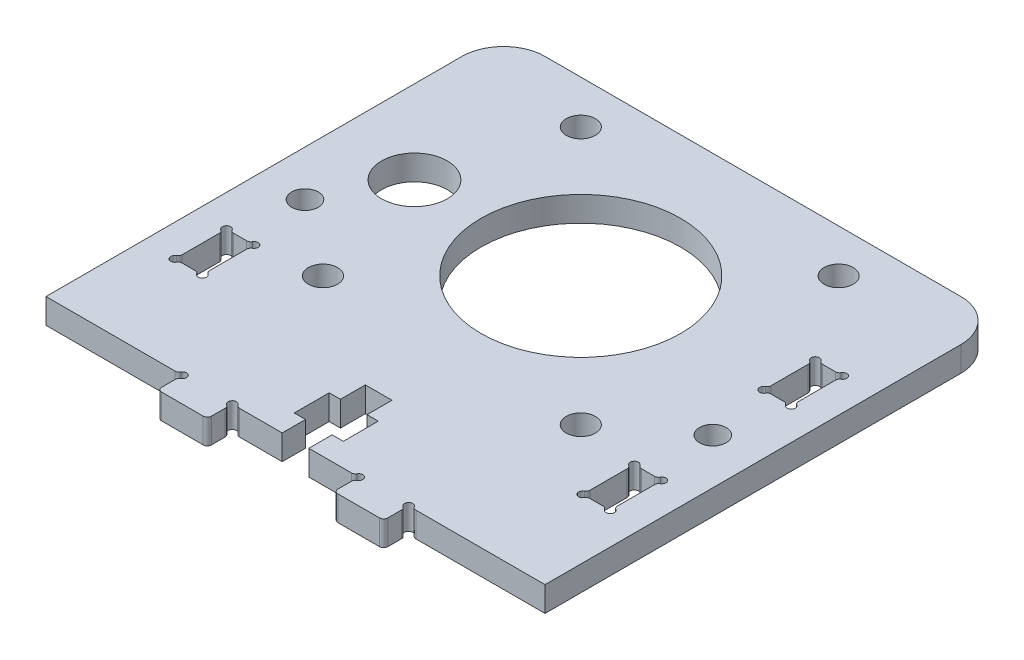
SolidWorks part; units mm, degrees
material "Plain Carbon Steel"
ref_plane "Front Plane" through (0, 0, 0) normal (0, 0, 1) x (1, 0, 0)
ref_plane "Top Plane" through (0, 0, 0) normal (0, 1, 0) x (1, 0, 0)
ref_plane "Right Plane" through (0, 0, 0) normal (1, 0, 0) x (0, 0, -1)
sketch "Sketch1" plane through (0, 0, 0) normal (0, 1, 0) x (1, 0, 0)
  line L0 (365.2434, 1060.953) -> (365.2434, 1056.485)
  line L1 (367.6773, 1061.819) -> (366.1094, 1061.819)
  line L3 (312.3734, 1022.1903) -> (327.9073, 1022.1903)
  line L4 (312.3734, 1072.1903) -> (312.3734, 1022.1903)
  line L5 (316.2034, 1039.1936) -> (316.2034, 1034.7256)
  line L6 (318.6373, 1040.0596) -> (317.0694, 1040.0596)
  line L7 (368.5433, 1034.7256) -> (368.5433, 1039.1936)
  line L8 (366.1094, 1033.8596) -> (367.6773, 1033.8596)
  line L9 (365.2434, 1039.1936) -> (365.2434, 1034.7256)
  line L10 (367.6773, 1040.0596) -> (366.1094, 1040.0596)
  line L14 (319.5033, 1034.7256) -> (319.5033, 1039.1936)
  line L15 (317.0694, 1033.8596) -> (318.6373, 1033.8596)
  line L16 (366.1094, 1055.619) -> (367.6773, 1055.619)
  line L17 (343.9733, 1022.1903) -> (349.1073, 1022.1903)
  line L18 (343.9733, 1024.9903) -> (343.9733, 1022.1903)
  line L19 (345.3233, 1024.9903) -> (343.9733, 1024.9903)
  line L20 (345.3233, 1029.1903) -> (345.3233, 1024.9903)
  line L21 (343.9733, 1029.1903) -> (345.3233, 1029.1903)
  line L22 (343.9733, 1032.1903) -> (343.9733, 1029.1903)
  line L23 (367.3733, 1077.1903) -> (317.3733, 1077.1903)
  line L24 (372.3733, 1022.1903) -> (372.3733, 1072.1903)
  line L25 (356.8394, 1022.1903) -> (372.3733, 1022.1903)
  line L26 (355.9733, 1019.6902) -> (355.9733, 1021.3243)
  line L27 (350.4733, 1019.1902) -> (355.4733, 1019.1902)
  line L28 (349.9733, 1021.3243) -> (349.9733, 1019.6902)
  line L29 (340.7733, 1032.1903) -> (343.9733, 1032.1903)
  line L30 (340.7733, 1029.1903) -> (340.7733, 1032.1903)
  line L31 (339.4233, 1029.1903) -> (340.7733, 1029.1903)
  line L32 (339.4233, 1024.9903) -> (339.4233, 1029.1903)
  line L33 (340.7733, 1024.9903) -> (339.4233, 1024.9903)
  line L34 (340.7733, 1022.1903) -> (340.7733, 1024.9903)
  line L35 (335.6394, 1022.1903) -> (340.7733, 1022.1903)
  line L36 (368.5433, 1056.485) -> (368.5433, 1060.953)
  line L37 (334.7733, 1019.6902) -> (334.7733, 1021.3243)
  line L38 (329.2733, 1019.1902) -> (334.2733, 1019.1902)
  line L39 (328.7733, 1021.3243) -> (328.7733, 1019.6902)
  line L40 (372.3733, 1022.1903) -> (312.3734, 1022.1903) construction
  line L41 (317.8533, 1047.1903) -> (317.8533, 1081.5508) construction
  line L42 (368.0078, 1047.1903) -> (368.0078, 1096.6784) construction
  line L43 (372.3733, 1047.8425) -> (312.3734, 1047.8425) construction
  line L44 (372.3733, 1047.1903) -> (312.3734, 1047.1903) construction
  line L45 (380.2472, 1037.1058) -> (356.8394, 1037.1058) construction
  line L46 (380.2472, 1058.9023) -> (356.8394, 1058.9023) construction
  line L47 (307.0334, 1058.9093) -> (325.3733, 1058.9093) construction
  line L48 (330.3637, 1037.1128) -> (308.6429, 1037.1128) construction
  line L49 (330.3637, 1051.8885) -> (308.6429, 1051.8885) construction
  line L50 (372.3733, 1036.9659) -> (312.3734, 1036.9659) construction
  line L51 (372.3733, 1058.719) -> (312.3734, 1058.719) construction
  line L52 (-657.6267, 1056.4903) -> (49342.3733, 1056.4903)
  line L53 (342.3733, 56.4903) -> (342.3733, 50056.4903)
  line L54 (325.3733, 51.4903) -> (325.3733, 50051.4903)
  line L55 (-674.6267, 1056.4903) -> (49325.3733, 1056.4903)
  line L56 (342.3733, 56.4903) -> (342.3733, 50056.4903) construction
  line L57 (322.3733, 51.4903) -> (322.3733, 50051.4903)
  arc A0 (317.3733, 1077.1903) -> (312.3734, 1072.1903) centre (317.3733, 1072.1903) ccw
  arc A1 (364.9934, 1056.052) -> (365.6764, 1055.369) centre (365.2434, 1055.619) ccw
  arc A2 (364.9934, 1056.052) -> (365.2434, 1056.485) centre (364.7434, 1056.485) ccw
  arc A3 (365.6764, 1062.069) -> (366.1094, 1061.819) centre (366.1094, 1062.319) ccw
  arc A5 (365.2434, 1060.953) -> (364.9934, 1061.386) centre (364.7434, 1060.953) ccw
  arc A6 (365.6764, 1062.069) -> (364.9934, 1061.386) centre (365.2434, 1061.819) ccw
  arc A7 (366.1094, 1055.619) -> (365.6764, 1055.369) centre (366.1094, 1055.119) ccw
  arc A8 (315.9534, 1034.2926) -> (316.2034, 1034.7256) centre (315.7034, 1034.7256) ccw
  arc A9 (316.2034, 1039.1936) -> (315.9534, 1039.6266) centre (315.7034, 1039.1936) ccw
  arc A10 (316.6364, 1040.3096) -> (315.9534, 1039.6266) centre (316.2034, 1040.0596) ccw
  arc A11 (316.6364, 1040.3096) -> (317.0694, 1040.0596) centre (317.0694, 1040.5596) ccw
  arc A12 (367.6773, 1061.819) -> (368.1103, 1062.069) centre (367.6773, 1062.319) ccw
  arc A13 (368.7933, 1039.6266) -> (368.1103, 1040.3096) centre (368.5433, 1040.0596) ccw
  arc A14 (368.7933, 1039.6266) -> (368.5433, 1039.1936) centre (369.0433, 1039.1936) ccw
  arc A15 (368.5433, 1034.7256) -> (368.7933, 1034.2926) centre (369.0433, 1034.7256) ccw
  arc A16 (368.1103, 1033.6096) -> (368.7933, 1034.2926) centre (368.5433, 1033.8596) ccw
  arc A17 (368.1103, 1033.6096) -> (367.6773, 1033.8596) centre (367.6773, 1033.3596) ccw
  arc A18 (366.1094, 1033.8596) -> (365.6764, 1033.6096) centre (366.1094, 1033.3596) ccw
  arc A19 (364.9934, 1034.2926) -> (365.6764, 1033.6096) centre (365.2434, 1033.8596) ccw
  arc A20 (364.9934, 1034.2926) -> (365.2434, 1034.7256) centre (364.7434, 1034.7256) ccw
  arc A21 (365.2434, 1039.1936) -> (364.9934, 1039.6266) centre (364.7434, 1039.1936) ccw
  arc A22 (365.6764, 1040.3096) -> (364.9934, 1039.6266) centre (365.2434, 1040.0596) ccw
  arc A23 (365.6764, 1040.3096) -> (366.1094, 1040.0596) centre (366.1094, 1040.5596) ccw
  arc A24 (367.6773, 1040.0596) -> (368.1103, 1040.3096) centre (367.6773, 1040.5596) ccw
  circle A35 centre (366.8933, 1047.8425) radius 1.6
  circle A36 centre (357.8733, 1071.9903) radius 1.75
  circle A37 centre (357.8733, 1040.9903) radius 1.75
  arc A39 (319.7533, 1039.6266) -> (319.0703, 1040.3096) centre (319.5033, 1040.0596) ccw
  arc A40 (319.7533, 1039.6266) -> (319.5033, 1039.1936) centre (320.0033, 1039.1936) ccw
  arc A41 (319.5033, 1034.7256) -> (319.7533, 1034.2926) centre (320.0033, 1034.7256) ccw
  arc A42 (319.0703, 1033.6096) -> (319.7533, 1034.2926) centre (319.5033, 1033.8596) ccw
  arc A43 (319.0703, 1033.6096) -> (318.6373, 1033.8596) centre (318.6373, 1033.3596) ccw
  arc A44 (315.9534, 1034.2926) -> (316.6364, 1033.6096) centre (316.2034, 1033.8596) ccw
  arc A45 (349.1073, 1022.1903) -> (349.5403, 1022.4403) centre (349.1073, 1022.6903) ccw
  arc A46 (318.6373, 1040.0596) -> (319.0703, 1040.3096) centre (318.6373, 1040.5596) ccw
  circle A47 centre (322.3733, 1056.4903) radius 3.95
  circle A48 centre (342.3733, 1056.4903) radius 12
  arc A49 (372.3733, 1072.1903) -> (367.3733, 1077.1903) centre (367.3733, 1072.1903) ccw
  arc A50 (356.4064, 1022.4403) -> (356.8394, 1022.1903) centre (356.8394, 1022.6903) ccw
  arc A51 (356.4064, 1022.4403) -> (355.7233, 1021.7573) centre (355.9733, 1022.1903) ccw
  arc A52 (355.9733, 1021.3243) -> (355.7233, 1021.7573) centre (355.4733, 1021.3243) ccw
  arc A53 (355.4733, 1019.1902) -> (355.9733, 1019.6902) centre (355.4733, 1019.6902) ccw
  arc A54 (349.9733, 1019.6902) -> (350.4733, 1019.1902) centre (350.4733, 1019.6902) ccw
  arc A55 (350.2233, 1021.7573) -> (349.9733, 1021.3243) centre (350.4733, 1021.3243) ccw
  arc A56 (350.2233, 1021.7573) -> (349.5403, 1022.4403) centre (349.9733, 1022.1903) ccw
  arc A57 (317.0694, 1033.8596) -> (316.6364, 1033.6096) centre (317.0694, 1033.3596) ccw
  arc A58 (327.9073, 1022.1903) -> (328.3403, 1022.4403) centre (327.9073, 1022.6903) ccw
  arc A59 (335.2063, 1022.4403) -> (335.6394, 1022.1903) centre (335.6394, 1022.6903) ccw
  circle A60 centre (326.8733, 1071.9903) radius 1.75
  circle A61 centre (326.8733, 1040.9903) radius 1.75
  circle A62 centre (317.8533, 1047.8495) radius 1.6
  arc A63 (368.7933, 1061.386) -> (368.1103, 1062.069) centre (368.5433, 1061.819) ccw
  arc A64 (368.5433, 1056.485) -> (368.7933, 1056.052) centre (369.0433, 1056.485) ccw
  arc A65 (335.2063, 1022.4403) -> (334.5233, 1021.7573) centre (334.7733, 1022.1903) ccw
  arc A66 (334.7733, 1021.3243) -> (334.5233, 1021.7573) centre (334.2733, 1021.3243) ccw
  arc A67 (368.7933, 1061.386) -> (368.5433, 1060.953) centre (369.0433, 1060.953) ccw
  arc A68 (328.7733, 1019.6902) -> (329.2733, 1019.1902) centre (329.2733, 1019.6902) ccw
  arc A69 (368.1103, 1055.369) -> (368.7933, 1056.052) centre (368.5433, 1055.619) ccw
  arc A70 (368.1103, 1055.369) -> (367.6773, 1055.619) centre (367.6773, 1055.119) ccw
  arc A71 (329.0233, 1021.7573) -> (328.3403, 1022.4403) centre (328.7733, 1022.1903) ccw
  arc A72 (334.2733, 1019.1902) -> (334.7733, 1019.6902) centre (334.2733, 1019.6902) ccw
  arc A73 (329.0233, 1021.7573) -> (328.7733, 1021.3243) centre (329.2733, 1021.3243) ccw
  point P193 (317.8533, 1047.8495)
  point P202 (368.5433, 1036.9596)
  point P205 (368.5433, 1058.719)
  point P211 (319.5033, 1036.9596)
  dimension "D5" = 24
  dimension "D3" = 14.7757
  dimension "D6" = 60
  dimension "D7" = 55
  dimension "D1" = 25
  dimension "D2" = 25.6522
  dimension "D4" = 36.5287
extrude "Boss-Extrude1" add sketch "Sketch1" along normal blind 3
